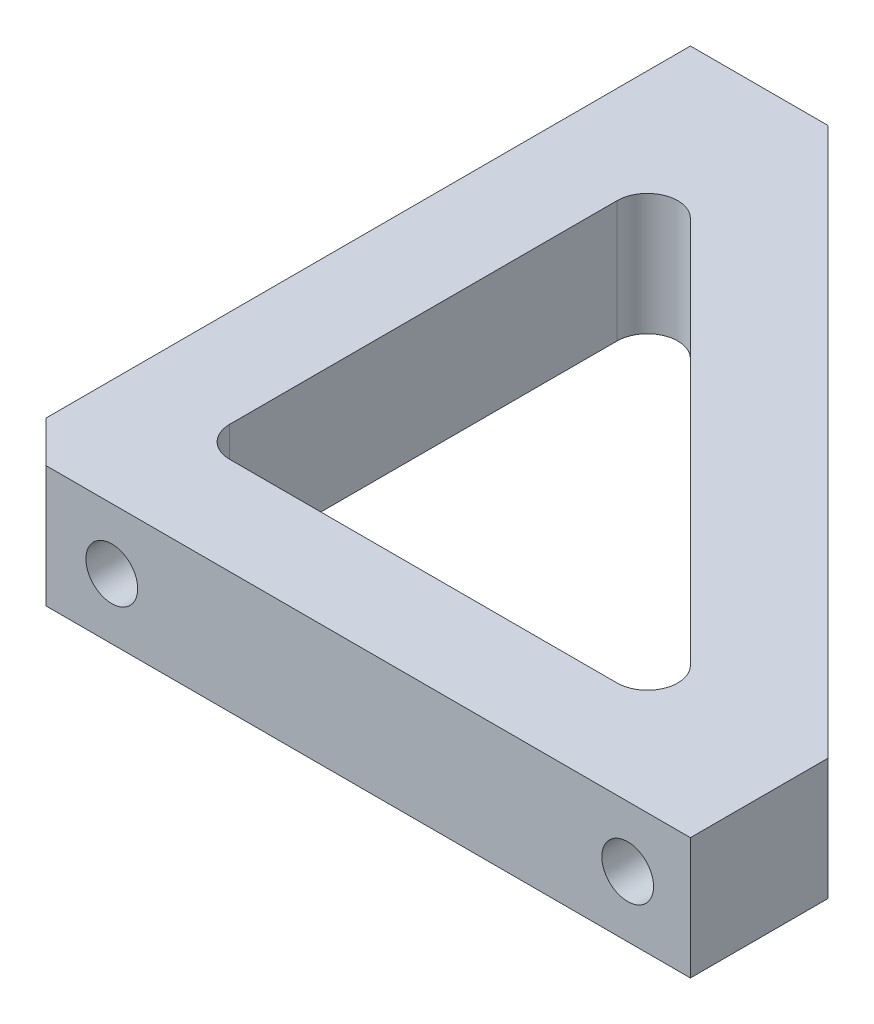
SolidWorks part; units mm, degrees
ref_plane "Front Plane" through (0, 0, 0) normal (0, 0, 1) x (1, 0, 0)
ref_plane "Top Plane" through (0, 0, 0) normal (0, 1, 0) x (1, 0, 0)
ref_plane "Right Plane" through (0, 0, 0) normal (1, 0, 0) x (0, 0, -1)
sketch "Sketch1" plane through (0, 0, 0) normal (0, 1, 0) x (1, 0, 0)
  line L0 (0, 0) -> (0, 35.814)
  line L1 (7.184, 35.814) -> (35.814, 7.184)
  line L2 (35.814, 0) -> (0, 0)
  line L3 (0, 35.814) -> (7.184, 35.814)
  line L4 (35.814, 7.184) -> (35.814, 0)
  line L5 (5.08, 30.7337) -> (5.08, 5.08)
  line L6 (5.08, 5.08) -> (30.7337, 5.08)
  line L7 (30.7337, 5.08) -> (5.08, 30.7337)
  dimension "D1" = 35.814
  dimension "D2" = 35.814
  dimension "D3" = 40.489
  dimension "D4" = 5.08
  dimension "D5" = 5.08
  dimension "D6" = 5.08
extrude "Boss-Extrude1" add sketch "Sketch1" along normal blind 6.35
fillet "Fillet1" radius 1.588 3 edges at (30.7337, 3.175, -5.08) (5.08, 3.175, -5.08) (5.08, 3.175, -30.7337)
sketch "Sketch2" plane through (0, 0, 0) normal (-1, 0, 0) x (0, 0, 1)
  line L0 (-5.588, 3.175) -> (-32.5374, 3.175) construction
  line L1 (0, 6.35) -> (0, 0) construction
  point P4 (0, 3.175)
  dimension "D1" = 26.9494
  dimension "D2" = 5.588
hole_wizard "Tap Drill for #6-32 Tap2" positions "Sketch6" profile "Sketch7" hole size "#6-32" standard "ANSI Inch"
sketch "Sketch6" plane through (0, 0, 0) normal (-1, 0, 0) x (0, 0, 1)
  point P0 (-5.588, 3.175)
  point P3 (-32.5374, 3.175)
sketch "Sketch7" plane through (0, 3.175, -5.588) normal (0, 1, 0) x (0, 0, 1)
  line L0 (0, 0) -> (0, 7.1627)
  line L1 (0, 7.1627) -> (1.3525, 6.35)
  line L2 (1.3525, 6.35) -> (1.3525, 0)
  line L5 (1.3525, 0) -> (0, 0)
  line L10 (0, 7.1627) -> (-1.3526, 6.35) construction
  line L11 (0, -6.35) -> (0, 107.95) construction
  dimension "Hole Dia." = 2.7051
  dimension "Hole Depth" = 6.35
  dimension "Drill Angle" = 118
sketch "Sketch3" plane through (0, 0, 0) normal (0, 0, 1) x (1, 0, 0)
  line L0 (32.5374, 3.175) -> (5.588, 3.175) construction
  line L1 (0, 6.35) -> (0, 0) construction
  line L2 (35.814, 6.35) -> (35.814, 0) construction
  point P6 (35.814, 3.175)
  dimension "D1" = 26.9494
  dimension "D2" = 5.588
hole_wizard "Tap Drill for #6-32 Tap1" positions "Sketch4" profile "Sketch5" hole size "#6-32" standard "ANSI Inch"
sketch "Sketch4" plane through (0, 0, 0) normal (0, 0, 1) x (1, 0, 0)
  point P0 (32.5374, 3.175)
  point P3 (5.588, 3.175)
sketch "Sketch5" plane through (32.5374, 3.175, 0) normal (1, 0, 0) x (0, -1, 0)
  line L0 (0, 0) -> (0, 7.1627)
  line L1 (0, 7.1627) -> (1.3525, 6.35)
  line L2 (1.3525, 6.35) -> (1.3525, 0)
  line L5 (1.3525, 0) -> (0, 0)
  line L10 (0, 7.1627) -> (-1.3526, 6.35) construction
  line L11 (0, -6.35) -> (0, 107.95) construction
  dimension "Hole Dia." = 2.7051
  dimension "Hole Depth" = 6.35
  dimension "Drill Angle" = 118
chamfer "Chamfer1" distance 2.155 angle 45 1 edges at (0, 3.175, 0)
